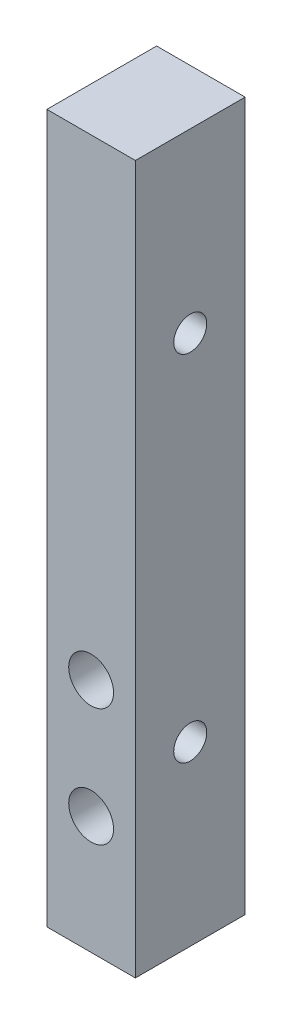
SolidWorks part; units mm, degrees
ref_plane "Front Plane" through (0, 0, 0) normal (0, 0, 1) x (1, 0, 0)
ref_plane "Top Plane" through (0, 0, 0) normal (0, 1, 0) x (1, 0, 0)
ref_plane "Right Plane" through (0, 0, 0) normal (1, 0, 0) x (0, 0, -1)
sketch "Sketch1" plane through (0, 0, 0) normal (0, 0, 1) x (1, 0, 0)
  line L1 (0, 0) -> (9.525, 0)
  line L2 (0, 0) -> (0, 76.2)
  line L3 (0, 76.2) -> (9.525, 76.2)
  line L4 (9.525, 0) -> (9.525, 76.2)
  dimension "D1" = 76.2
  dimension "D2" = 9.525
extrude "Boss-Extrude1" add sketch "Sketch1" along normal blind 11.811
sketch "Sketch2" plane through (0, 0, 0) normal (-1, 0, 0) x (0, 0, 1)
  line L0 (5.9055, 76.2) -> (5.9055, 0) construction
  line L1 (11.811, 76.2) -> (0, 76.2) construction
  line L2 (11.811, 0) -> (0, 0) construction
  circle A0 centre (5.9055, 57.15) radius 1.778
  circle A1 centre (5.9055, 19.05) radius 1.778
  dimension "D1" = 3.556
  dimension "D2" = 38.1
  dimension "D5" = 19.05
extrude "Cut-Extrude1" cut sketch "Sketch2" against normal through all
sketch "Sketch3" plane through (0, 0, 0) normal (0, 0, -1) x (-1, 0, 0)
  line L0 (0, 0) -> (-9.525, 0) construction
  line L1 (-4.7625, 0) -> (-4.7625, 32.9124) construction
  circle A0 centre (-4.7625, 25.4) radius 2.413
  circle A1 centre (-4.7625, 12.7) radius 2.413
  dimension "D1" = 4.826
  dimension "D2" = 12.7
  dimension "D3" = 12.7
extrude "Cut-Extrude2" cut sketch "Sketch3" against normal through all
